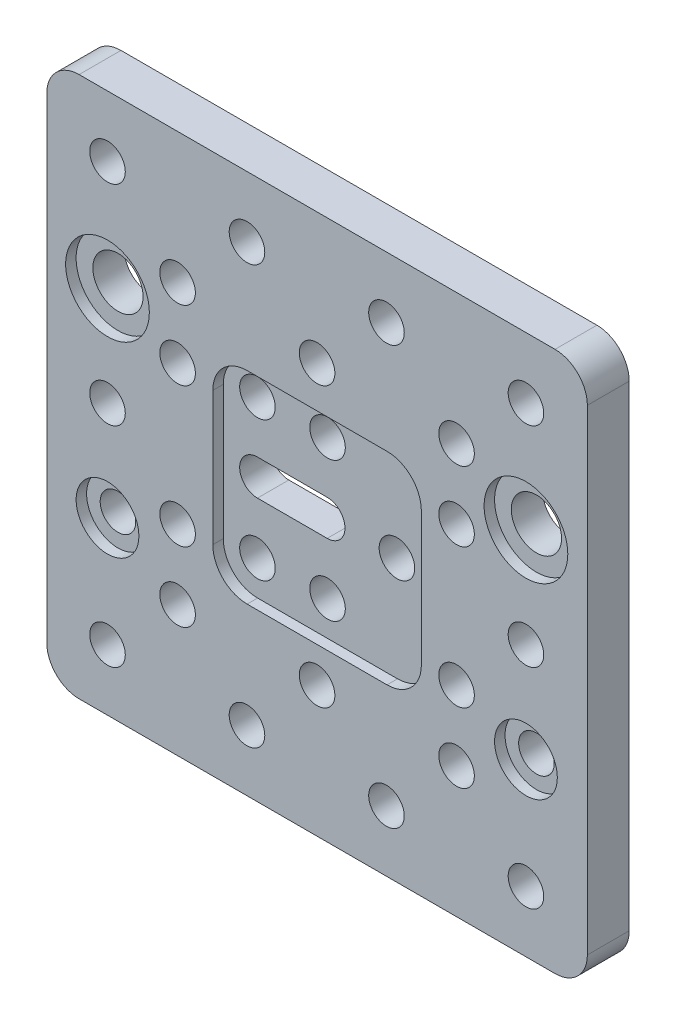
SolidWorks part; units mm, degrees
ref_plane "Front Plane" through (0, 0, 0) normal (0, 0, 1) x (1, 0, 0)
ref_plane "Top Plane" through (0, 0, 0) normal (0, 1, 0) x (1, 0, 0)
ref_plane "Right Plane" through (0, 0, 0) normal (1, 0, 0) x (0, 0, -1)
sketch "Sketch1" plane through (0, 0, 0) normal (0, 0, 1) x (1, 0, 0)
  line L0 (38.755, 38.7595) -> (38.755, -38.7595)
  line L1 (-38.755, -38.7595) -> (38.755, -38.7595)
  line L2 (-38.755, -38.7595) -> (-38.755, 38.7595)
  line L3 (-38.755, 38.7595) -> (38.755, 38.7595)
  line L4 (0, -42.6355) -> (0, 42.6355) construction
  line L5 (42.6305, 0) -> (-42.6305, 0) construction
  circle A0 centre (-30.05, 30.0005) radius 2.55
  circle A1 centre (-10.05, 30.0005) radius 2.55
  circle A2 centre (-10.05, -29.9995) radius 2.55
  circle A3 centre (0, 20) radius 2.55
  circle A4 centre (0, 10) radius 2.55
  circle A5 centre (-10.05, 10) radius 2.55
  circle A6 centre (9.95, 30.0005) radius 2.55
  circle A7 centre (9.95, -29.9995) radius 2.55
  circle A8 centre (-10.05, -10) radius 2.55
  circle A9 centre (9.95, 0.0005) radius 2.55
  circle A10 centre (-30.05, -29.9995) radius 2.55
  circle A11 centre (-30.05, -14.2495) radius 2.55
  circle A12 centre (-30.05, 0.0005) radius 2.55
  circle A13 centre (-30.05, 14.2505) radius 2.55
  circle A14 centre (0, -10) radius 2.55
  circle A15 centre (29.95, 30.0005) radius 2.55
  circle A16 centre (29.95, -29.9995) radius 2.55
  circle A17 centre (29.95, -14.2495) radius 2.55
  circle A18 centre (29.95, 0.0005) radius 2.55
  circle A19 centre (29.95, 14.2505) radius 2.55
  circle A20 centre (-10.05, 14.2505) radius 2.55 [skipped]
  circle A21 centre (9.95, 14.2505) radius 2.55 [skipped]
  circle A22 centre (-10.05, -14.2495) radius 2.55 [skipped]
  circle A23 centre (9.95, -14.2495) radius 2.55 [skipped]
  circle A24 centre (-10.05, 0.0005) radius 2.55 [skipped]
  circle A25 centre (0, -20) radius 2.55
  circle A26 centre (20, 20) radius 2.55
  circle A27 centre (20, 10) radius 2.55
  circle A28 centre (20, -10) radius 2.55
  circle A29 centre (20, -20) radius 2.55
  circle A30 centre (-20, 20) radius 2.55
  circle A31 centre (-20, 10) radius 2.55
  circle A32 centre (-20, -10) radius 2.55
  circle A33 centre (-20, -20) radius 2.55
  dimension "D3" = 5.1
  dimension "D5" = 8.705
  dimension "D7" = 14.25
  dimension "D8" = 15.75
  dimension "D9" = 0
  dimension "D10" = 14.25
  dimension "D11" = 0
  dimension "D12" = 15.75
  dimension "D13" = 0
  dimension "D17" = 5.1
  dimension "D18" = 20
  dimension "D19" = 10
  dimension "D20" = 0
  dimension "D21" = 40
  dimension "D22" = 20
  dimension "D23" = 0
  dimension "D24" = 10.05
  dimension "D1" = 77.519
  dimension "D2" = 77.51
  dimension "D4" = 38.76
  dimension "D6" = 0
  dimension "D15" = 38.755
  dimension "D16" = 38.7595
  dimension "D14" = 4
  dimension "D25" = 2
  dimension "D26" = 2
extrude "Boss-Extrude1" add sketch "Sketch1" along normal blind 6
sketch "Sketch2" plane through (0, 0, 6) normal (0, 0, 1) x (1, 0, 0)
  line L0 (3.3, 0) -> (-3.3, 0) construction
  line L1 (-10.05, 2.55) -> (-0.05, 2.55)
  line L2 (-10.05, -2.55) -> (-0.05, -2.55)
  arc A0 (-10.05, 2.55) -> (-10.05, -2.55) centre (-10.05, 0) ccw
  arc A1 (-0.05, -2.55) -> (-0.05, 2.55) centre (-0.05, 0) ccw
  circle A2 centre (9.95, 0.0005) radius 2.55 construction
  dimension "D1" = 5.1
  dimension "D2" = 10
  dimension "D3" = 10
extrude "Cut-Extrude1" cut sketch "Sketch2" against normal blind 6
fillet "Fillet1" radius 4.635 4 edges at (38.755, -38.7595, 3) (-38.755, -38.7595, 3) (-38.755, 38.7595, 3) (38.755, 38.7595, 3)
sketch "Sketch3" plane through (0, 0, 6) normal (0, 0, 1) x (1, 0, 0)
  line L0 (0, -3.3) -> (0, 3.3) construction
  line L1 (-10.03, 14.05) -> (10.03, 14.05)
  line L2 (-14.951, 9.129) -> (-14.951, -10.029)
  line L3 (-10.03, -14.95) -> (10.03, -14.95)
  line L4 (14.951, 9.129) -> (14.951, -10.029)
  line L5 (3.3, 0) -> (-3.3, 0) construction
  arc A0 (-14.951, -10.029) -> (-10.03, -14.95) centre (-10.03, -10.029) ccw
  arc A1 (10.03, -14.95) -> (14.951, -10.029) centre (10.03, -10.029) ccw
  arc A2 (10.03, 14.05) -> (14.951, 9.129) centre (10.03, 9.129) cw
  arc A3 (-10.03, 14.05) -> (-14.951, 9.129) centre (-10.03, 9.129) ccw
  dimension "D1" = 4.921
  dimension "D2" = 29.902
  dimension "D3" = 29
  dimension "D4" = 14.951
  dimension "D5" = 14.95
extrude "Cut-Extrude2" cut sketch "Sketch3" against normal blind 1.5
sketch "Sketch4" plane through (0, 0, 6) normal (0, 0, 1) x (1, 0, 0)
  circle A0 centre (-30.05, -14.2495) radius 4.5
  circle A1 centre (29.95, -14.2495) radius 4.5
  circle A3 centre (-30.05, 14.2505) radius 6
  circle A5 centre (29.95, 14.2505) radius 6
  dimension "D1" = 9
  dimension "D2" = 9
  dimension "D3" = 12
  dimension "D4" = 12
extrude "Cut-Extrude3" cut sketch "Sketch4" against normal blind 1.5
sketch "Sketch5" plane through (0, 0, 6) normal (0, 0, 1) x (1, 0, 0)
  circle A0 centre (-30.05, 14.2505) radius 3.6
  circle A1 centre (29.95, 14.2505) radius 3.6
  dimension "D1" = 7.2
  dimension "D2" = 7.2
extrude "Cut-Extrude4" cut sketch "Sketch5" against normal through all
